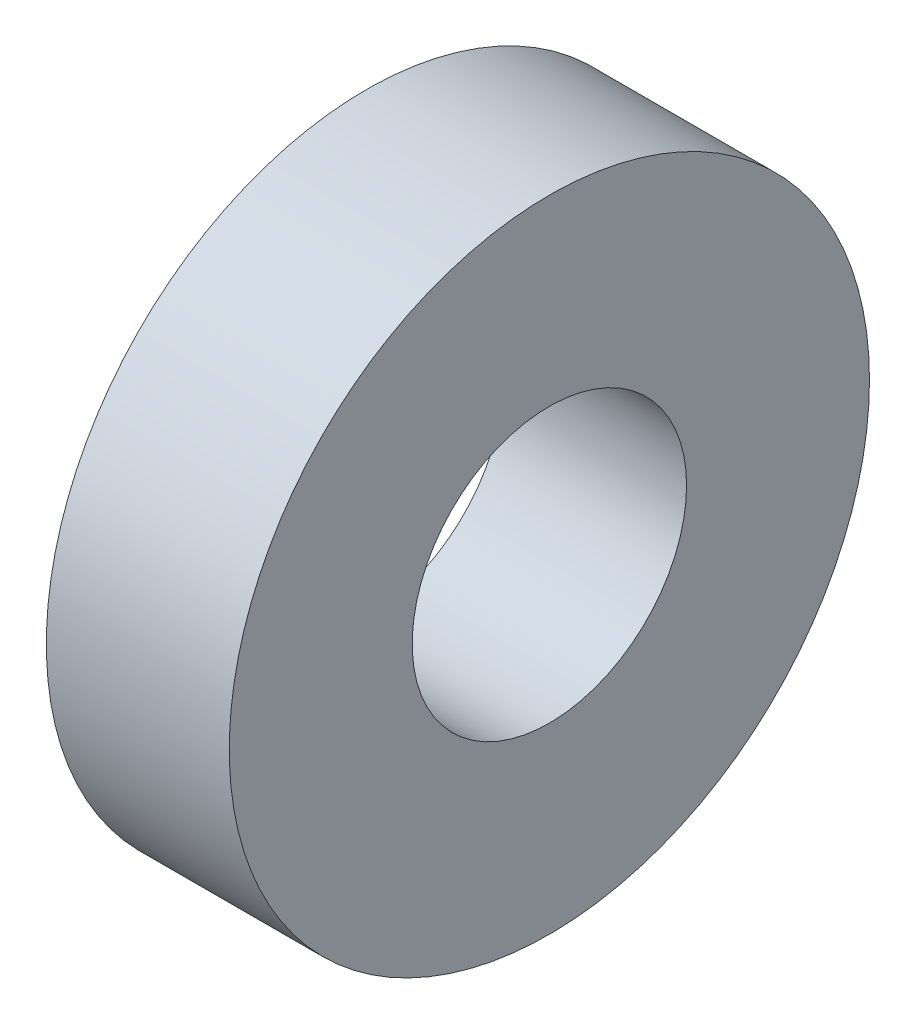
SolidWorks part; units mm, degrees
ref_plane "Front Plane" through (0, 0, 0) normal (0, 0, 1) x (1, 0, 0)
ref_plane "Top Plane" through (0, 0, 0) normal (0, 1, 0) x (1, 0, 0)
ref_plane "Right Plane" through (0, 0, 0) normal (1, 0, 0) x (0, 0, -1)
sketch "Sketch1" plane through (0, 0, 0) normal (1, 0, 0) x (0, 0, -1)
  circle A0 centre (0, 0) radius 14
  circle A1 centre (0, 0) radius 6
  dimension "D1" = 28
  dimension "D2" = 12
extrude "Boss-Extrude1" add sketch "Sketch1" along normal blind 8 contours A0 A1
